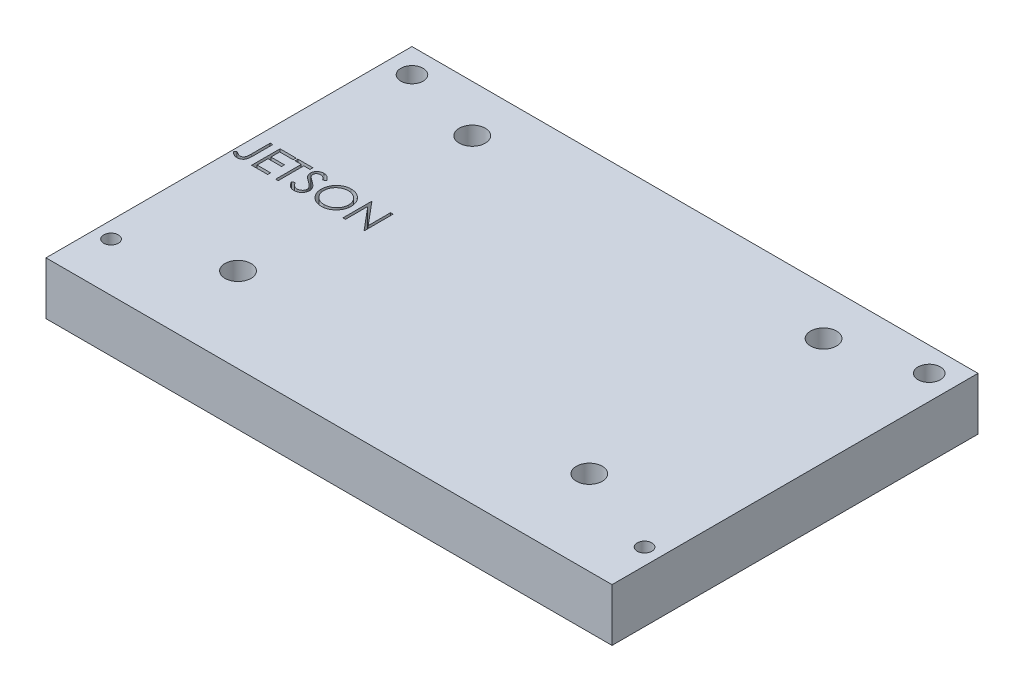
SolidWorks part; units mm, degrees
ref_plane "Front Plane" through (0, 0, 0) normal (0, 0, 1) x (1, 0, 0)
ref_plane "Top Plane" through (0, 0, 0) normal (0, 1, 0) x (1, 0, 0)
ref_plane "Right Plane" through (0, 0, 0) normal (1, 0, 0) x (0, 0, -1)
sketch "Sketch1" plane through (0, 0, 0) normal (0, 1, 0) x (1, 0, 0)
  line L1 (-2, -6) -> (67.6, -6)
  line L2 (-2, -6) -> (-2, 39)
  line L3 (-2, 39) -> (67.6, 39)
  line L4 (67.6, -6) -> (67.6, 39)
  circle A0 centre (0, 0) radius 0.9
  circle A1 centre (1, 36) radius 1.375
  circle A2 centre (65.6, 0) radius 0.9
  circle A3 centre (64.6, 36) radius 1.375
  circle A4 centre (11.2, 4.41) radius 1.6
  circle A5 centre (11.2, 33.21) radius 1.6
  circle A6 centre (54.4, 33.21) radius 1.6
  circle A7 centre (54.4, 4.41) radius 1.6
  dimension "D1" = 1.8
  dimension "D2" = 2.75
  dimension "D11" = 2.75
  dimension "D12" = 1.8
  dimension "D13" = 65.6
  dimension "D17" = 3.2
  dimension "D18" = 3.2
  dimension "D21" = 3.2
  dimension "D22" = 3.2
  dimension "D3" = 36
  dimension "D4" = 6
  dimension "D5" = 39
  dimension "D6" = 1
  dimension "D7" = 2
  dimension "D8" = 67.6
  dimension "D9" = 2
  dimension "D10" = 64.6
  dimension "D14" = 36
  dimension "D15" = 11.2
  dimension "D16" = 4.41
  dimension "D19" = 33.21
  dimension "D20" = 11.2
  dimension "D23" = 33.21
  dimension "D24" = 54.4
  dimension "D25" = 54.4
  dimension "D26" = 4.41
extrude "Boss-Extrude1" add sketch "Sketch1" along normal blind 6.48
sketch "Sketch2" plane through (0, 6.48, 0) normal (0, 1, 0) x (1, 0, 0)
  line L0 (-2, 16.5) -> (67.6, 16.5) construction
  line L1 (-2, 39) -> (-2, -6) construction
  line L2 (67.6, -6) -> (67.6, 39) construction
  text T0 "JETSON "
extrude "Cut-Extrude1" cut sketch "Sketch2" against normal through all
